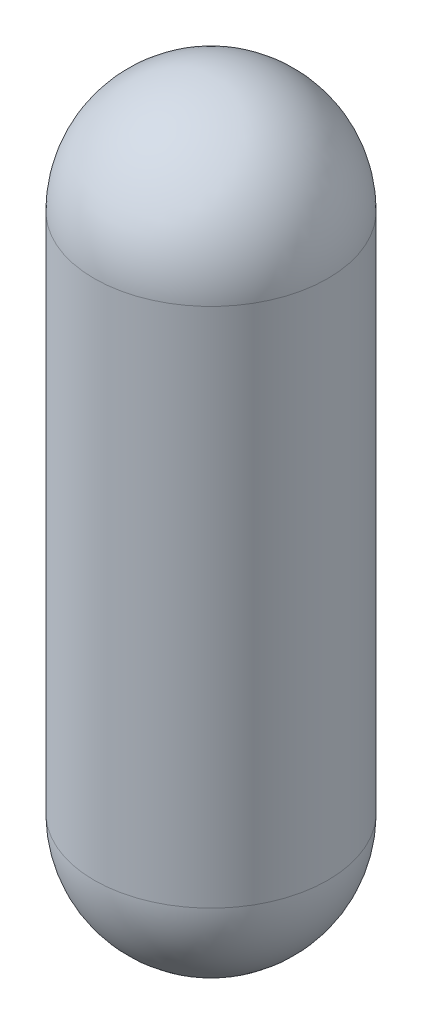
SolidWorks part; units mm, degrees
material "AISI 316 Annealed Stainless Steel Bar (SS)"
ref_plane "Front Plane" through (0, 0, 0) normal (0, 0, 1) x (1, 0, 0)
ref_plane "Top Plane" through (0, 0, 0) normal (0, 1, 0) x (1, 0, 0)
ref_plane "Right Plane" through (0, 0, 0) normal (1, 0, 0) x (0, 0, -1)
sketch "Sketch1" plane through (0, 0, 0) normal (0, 0, 1) x (1, 0, 0)
  line L0 (-82.55, -82.55) -> (-82.55, -450.85)
  line L1 (0, -450.85) -> (0, -82.55) construction
  line L2 (0, -533.4) -> (0, 0)
  arc A0 (0, 0) -> (-82.55, -82.55) centre (0, -82.55) ccw
  arc A1 (-82.55, -450.85) -> (0, -533.4) centre (0, -450.85) ccw
  dimension "D1" = 82.55
  dimension "D2" = 533.4
revolve "Revolve1" add sketch "Sketch1" angle 360 about L2
